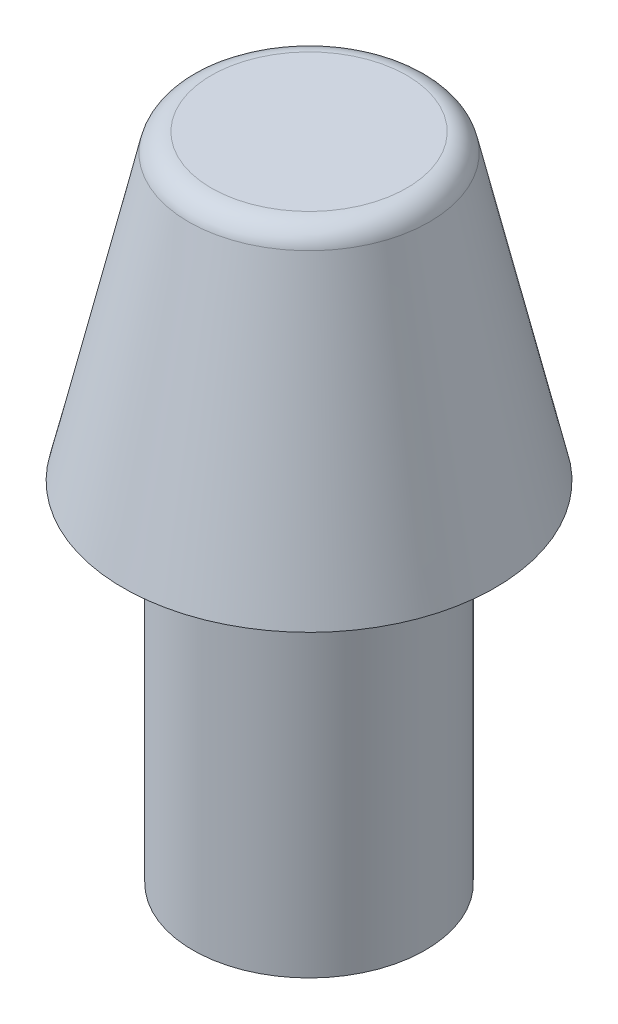
SolidWorks part; units mm, degrees
ref_plane "Front Plane" through (0, 0, 0) normal (0, 0, 1) x (1, 0, 0)
ref_plane "Top Plane" through (0, 0, 0) normal (0, 1, 0) x (1, 0, 0)
ref_plane "Right Plane" through (0, 0, 0) normal (1, 0, 0) x (0, 0, -1)
sketch "Sketch1" plane through (0, 0, 0) normal (0, 0, 1) x (1, 0, 0)
  line L0 (0, 0) -> (0, 7)
  line L1 (0, 0) -> (1.25, 0)
  line L2 (1.25, 0) -> (1.25, 3.75)
  line L3 (1.25, 3.75) -> (2, 3.75)
  line L4 (0, 7) -> (1.0511, 7)
  line L5 (1.2947, 6.8062) -> (2, 3.75)
  arc A0 (1.0511, 7) -> (1.2947, 6.8062) centre (1.0511, 6.75) cw
  point P9 (1.25, 7)
  dimension "D6" = 0.25
  dimension "D1" = 7
  dimension "D2" = 1.25
  dimension "D3" = 3.75
  dimension "D4" = 0.75
  dimension "D5" = 1.25
revolve "Revolve1" add sketch "Sketch1" angle 360 about L0
